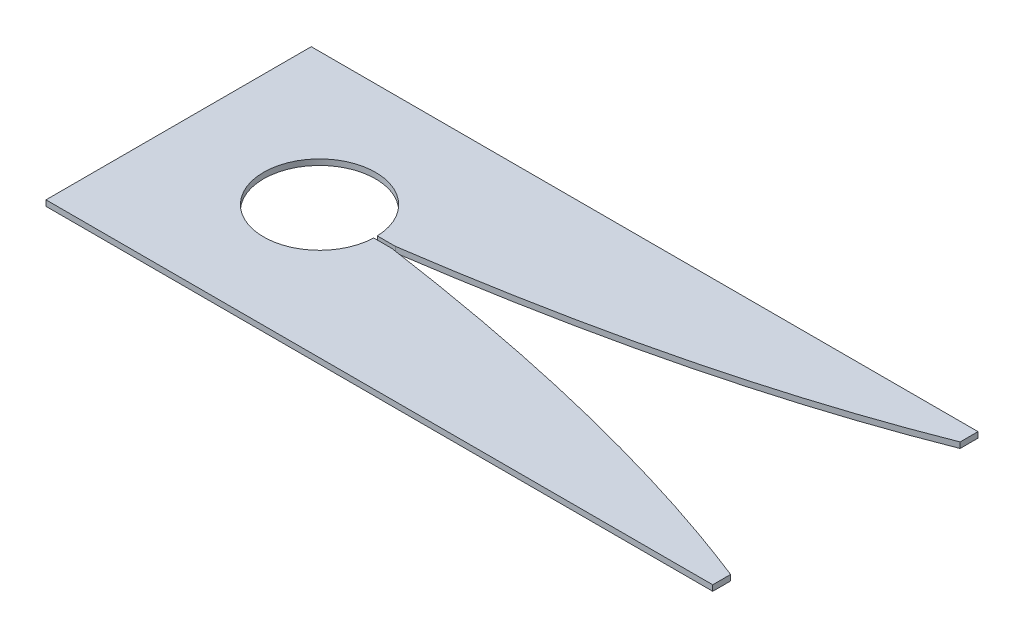
SolidWorks part; units mm, degrees
ref_plane "Front" through (0, 0, 0) normal (0, 0, 1) x (1, 0, 0)
ref_plane "Top" through (0, 0, 0) normal (0, 1, 0) x (1, 0, 0)
ref_plane "Right" through (0, 0, 0) normal (1, 0, 0) x (0, 0, -1)
sketch "Sketch1" plane through (0, 0, 0) normal (0, 1, 0) x (1, 0, 0)
  line L0 (-92.9999, -37.0001) -> (92.9999, -37.0001)
  line L1 (-92.9999, -37.0001) -> (-92.9999, 37.0001)
  line L2 (92.9999, -37.0001) -> (92.9999, 37.0001)
  line L3 (-92.9999, 37.0001) -> (92.9999, 37.0001)
  line L4 (-92.9999, -37.0001) -> (92.9999, 37.0001) construction
  line L5 (92.9999, -37.0001) -> (-92.9999, 37.0001) construction
  line L6 (92.964, 31.75) -> (92.964, -31.75)
  line L7 (-33.02, -0.9971) -> (-37.093, -0.9971)
  line L8 (-37.093, -0.9971) -> (-37.093, 0.9971)
  line L9 (-37.093, 0.9971) -> (-33.02, 0.9971)
  spline S0 degree 4 poles (-45.6197, -0.7148) (-45.419, -0.6888) (-45.0217, -0.6373) (-44.2575, -0.5383) (-42.6269, -0.3238) (-40.5686, -0.051) (-38.0308, 0.2948) (-35.9146, 0.5872) (-33.3422, 0.9506) (-32.1764, 1.1175) (-29.311, 1.5318) (-27.5556, 1.794) (-24.9918, 2.1776) (-22.9161, 2.4977) (-20.5474, 2.8657) (-18.3562, 3.2147) (-16.0618, 3.5849) (-13.8271, 3.953) (-10.9989, 4.4264) (-7.6266, 5.0049) (-3.6838, 5.7012) (0.8099, 6.5235) (5.3023, 7.3751) (9.7867, 8.2559) (14.2664, 9.1672) (18.7388, 10.1098) (23.2047, 11.0847) (28.1443, 12.2016) (33.0741, 13.3618) (37.9931, 14.5667) (42.9005, 15.8179) (47.32, 16.9846) (51.7292, 18.1898) (56.1275, 19.4344) (59.9658, 20.5588) (63.2481, 21.5485) (66.5238, 22.5591) (69.7932, 23.5911) (73.0534, 24.6499) (76.0345, 25.6462) (78.1969, 26.3834) (79.8188, 26.9427) (81.434, 27.5058) (83.3257, 28.1752) (85.4657, 28.9448) (87.3602, 29.6383) (88.9415, 30.2247) (90.3224, 30.7433) (91.291, 31.1093) (92.7461, 31.6655) (93.5084, 31.9594) (95.4183, 32.7008) (96.5717, 33.1584) (98.2705, 33.8329) (99.6393, 34.3874) (101.2218, 35.0314) (102.4786, 35.5521) (103.6359, 36.0337) (104.3677, 36.342) (104.7445, 36.5009) (104.9341, 36.581) knots 0 0 0 0 0 0.005108 0.010215 0.02043 0.040861 0.061291 0.071506 0.081722 0.096411 0.111101 0.125791 0.140481 0.155171 0.169861 0.18455 0.19924 0.21393 0.22862 0.258 0.287379 0.316759 0.346139 0.375518 0.404898 0.434278 0.463657 0.493037 0.535103 0.564483 0.593863 0.623242 0.652622 0.682002 0.711381 0.726071 0.740761 0.770141 0.799521 0.81421 0.821555 0.8289 0.84359 0.85828 0.87297 0.88766 0.895004 0.902349 0.909694 0.917039 0.927346 0.937653 0.94796 0.958267 0.9687 0.979133 0.989567 0.994783 1 1 1 1 1 construction
  spline S1 degree 4 poles (-33.02, 0.9971) (-32.5475, 1.0646) (-31.6372, 1.1955) (-29.311, 1.5318) (-27.5556, 1.794) (-24.9918, 2.1776) (-22.9161, 2.4977) (-20.5474, 2.8657) (-18.3562, 3.2147) (-16.0618, 3.5849) (-13.8271, 3.953) (-10.9989, 4.4264) (-7.6266, 5.0049) (-3.6838, 5.7012) (0.8099, 6.5235) (5.3023, 7.3751) (9.7867, 8.2559) (14.2664, 9.1672) (18.7388, 10.1098) (23.2047, 11.0847) (28.1443, 12.2016) (33.0741, 13.3618) (37.9931, 14.5667) (42.9005, 15.8179) (47.32, 16.9846) (51.7292, 18.1898) (56.1275, 19.4344) (59.9658, 20.5588) (63.2481, 21.5485) (66.5238, 22.5591) (69.7932, 23.5911) (73.0534, 24.6499) (76.0345, 25.6462) (78.1969, 26.3834) (79.8188, 26.9427) (81.434, 27.5058) (83.3257, 28.1752) (85.4657, 28.9448) (87.3602, 29.6383) (88.9415, 30.2247) (90.3224, 30.7433) (91.291, 31.1093) (92.2824, 31.4882) (92.7413, 31.6643) (92.964, 31.75) knots 0.081722 0.081722 0.081722 0.081722 0.081722 0.096411 0.111101 0.125791 0.140481 0.155171 0.169861 0.18455 0.19924 0.21393 0.22862 0.258 0.287379 0.316759 0.346139 0.375518 0.404898 0.434278 0.463657 0.493037 0.535103 0.564483 0.593863 0.623242 0.652622 0.682002 0.711381 0.726071 0.740761 0.770141 0.799521 0.81421 0.821555 0.8289 0.84359 0.85828 0.87297 0.88766 0.895004 0.902349 0.909694 0.917039 0.917039 0.917039 0.917039 0.917039
  spline S2 degree 4 poles (-45.6197, 0.7148) (-45.419, 0.6888) (-45.0217, 0.6373) (-44.2575, 0.5383) (-42.6269, 0.3238) (-40.5686, 0.051) (-38.0308, -0.2948) (-35.9146, -0.5872) (-33.3422, -0.9506) (-32.1764, -1.1175) (-29.311, -1.5318) (-27.5556, -1.794) (-24.9918, -2.1776) (-22.9161, -2.4977) (-20.5474, -2.8657) (-18.3562, -3.2147) (-16.0618, -3.5849) (-13.8271, -3.953) (-10.9989, -4.4264) (-7.6266, -5.0049) (-3.6838, -5.7012) (0.8099, -6.5235) (5.3023, -7.3751) (9.7867, -8.2559) (14.2664, -9.1672) (18.7388, -10.1098) (23.2047, -11.0847) (28.1443, -12.2016) (33.0741, -13.3618) (37.9931, -14.5667) (42.9005, -15.8179) (47.32, -16.9846) (51.7292, -18.1898) (56.1275, -19.4344) (59.9658, -20.5588) (63.2481, -21.5485) (66.5238, -22.5591) (69.7932, -23.5911) (73.0534, -24.6499) (76.0345, -25.6462) (78.1969, -26.3834) (79.8188, -26.9427) (81.434, -27.5058) (83.3257, -28.1752) (85.4657, -28.9448) (87.3602, -29.6383) (88.9415, -30.2247) (90.3224, -30.7433) (91.291, -31.1093) (92.7461, -31.6655) (93.5084, -31.9594) (95.4183, -32.7008) (96.5717, -33.1584) (98.2705, -33.8329) (99.6393, -34.3874) (101.2218, -35.0314) (102.4786, -35.5521) (103.6359, -36.0337) (104.3677, -36.342) (104.7445, -36.5009) (104.9341, -36.581) knots 0 0 0 0 0 0.005108 0.010215 0.02043 0.040861 0.061291 0.071506 0.081722 0.096411 0.111101 0.125791 0.140481 0.155171 0.169861 0.18455 0.19924 0.21393 0.22862 0.258 0.287379 0.316759 0.346139 0.375518 0.404898 0.434278 0.463657 0.493037 0.535103 0.564483 0.593863 0.623242 0.652622 0.682002 0.711381 0.726071 0.740761 0.770141 0.799521 0.81421 0.821555 0.8289 0.84359 0.85828 0.87297 0.88766 0.895004 0.902349 0.909694 0.917039 0.927346 0.937653 0.94796 0.958267 0.9687 0.979133 0.989567 0.994783 1 1 1 1 1 construction
  spline S3 degree 4 poles (-33.02, -0.9971) (-32.5475, -1.0646) (-31.6372, -1.1955) (-29.311, -1.5318) (-27.5556, -1.794) (-24.9918, -2.1776) (-22.9161, -2.4977) (-20.5474, -2.8657) (-18.3562, -3.2147) (-16.0618, -3.5849) (-13.8271, -3.953) (-10.9989, -4.4264) (-7.6266, -5.0049) (-3.6838, -5.7012) (0.8099, -6.5235) (5.3023, -7.3751) (9.7867, -8.2559) (14.2664, -9.1672) (18.7388, -10.1098) (23.2047, -11.0847) (28.1443, -12.2016) (33.0741, -13.3618) (37.9931, -14.5667) (42.9005, -15.8179) (47.32, -16.9846) (51.7292, -18.1898) (56.1275, -19.4344) (59.9658, -20.5588) (63.2481, -21.5485) (66.5238, -22.5591) (69.7932, -23.5911) (73.0534, -24.6499) (76.0345, -25.6462) (78.1969, -26.3834) (79.8188, -26.9427) (81.434, -27.5058) (83.3257, -28.1752) (85.4657, -28.9448) (87.3602, -29.6383) (88.9415, -30.2247) (90.3224, -30.7433) (91.291, -31.1093) (92.2824, -31.4882) (92.7413, -31.6643) (92.964, -31.75) knots 0.081722 0.081722 0.081722 0.081722 0.081722 0.096411 0.111101 0.125791 0.140481 0.155171 0.169861 0.18455 0.19924 0.21393 0.22862 0.258 0.287379 0.316759 0.346139 0.375518 0.404898 0.434278 0.463657 0.493037 0.535103 0.564483 0.593863 0.623242 0.652622 0.682002 0.711381 0.726071 0.740761 0.770141 0.799521 0.81421 0.821555 0.8289 0.84359 0.85828 0.87297 0.88766 0.895004 0.902349 0.909694 0.917039 0.917039 0.917039 0.917039 0.917039
  point P1 (0, 0)
  dimension "D1" = 74.0001
  dimension "D2" = 185.9999
extrude "Boss-Extrude3" add sketch "Sketch1" along normal blind 1.5875 contours L0 L2 L3 L1
sketch "Sketch4" plane through (0, 1.5875, 0) normal (0, 1, 0) x (1, 0, 0)
  line L0 (-33.02, 0.5) -> (-38.0763, 0.5)
  line L1 (92.964, 31.9999) -> (94.1908, 31.9999)
  line L2 (-38.0763, -0.5) -> (-33.02, -0.5)
  line L3 (94.1908, 31.9999) -> (94.1908, -31.9999)
  line L4 (94.1908, -31.9999) -> (92.964, -31.9999)
  arc A0 (-38.0763, 0.5) -> (-38.0763, -0.5) centre (-53.6893, 0) ccw
  spline S0 degree 4 poles (-45.6216, -1.2538) (-45.4152, -1.2264) (-45.0124, -1.1728) (-44.2886, -1.0772) (-42.5574, -0.8429) (-41.0656, -0.6424) (-38.7059, -0.3125) (-36.8776, -0.0578) (-33.8387, 0.38) (-32.6102, 0.5588) (-29.371, 1.0389) (-27.4951, 1.3252) (-25.0001, 1.7081) (-22.8724, 2.0437) (-20.5264, 2.4175) (-18.3124, 2.7785) (-16.0227, 3.1572) (-13.7765, 3.5362) (-10.9454, 4.0219) (-6.4335, 4.815) (-1.3567, 5.7445) (4.2702, 6.8248) (11.0135, 8.1823) (16.6209, 9.3655) (22.2175, 10.6032) (28.2313, 11.9974) (33.1186, 13.1762) (37.9946, 14.3998) (42.8589, 15.6697) (47.2851, 16.8662) (51.7006, 18.1021) (56.1045, 19.3784) (59.9473, 20.5313) (63.233, 21.5458) (65.9655, 22.4093) (68.148, 23.1109) (70.8719, 24.0017) (73.5891, 24.9108) (76.0299, 25.7463) (78.1934, 26.5017) (79.8162, 27.0749) (81.432, 27.652) (83.3244, 28.3378) (85.4651, 29.1263) (87.3598, 29.8368) (88.9416, 30.4376) (90.3222, 30.9687) (91.2914, 31.3438) (92.7462, 31.9134) (93.5086, 32.2146) (95.4193, 32.9742) (96.5725, 33.4429) (98.2719, 34.1339) (99.6403, 34.7018) (101.2229, 35.3615) (102.4792, 35.8946) (103.6365, 36.388) (104.3678, 36.7035) (104.7446, 36.8663) (104.9341, 36.9483) knots 0 0 0 0 0 0.005102 0.010204 0.020408 0.040816 0.05102 0.061223 0.081631 0.096344 0.111056 0.125769 0.140481 0.155194 0.169906 0.184619 0.199331 0.214044 0.228757 0.258182 0.317032 0.346457 0.375882 0.434732 0.464157 0.493582 0.534357 0.563782 0.593207 0.622632 0.652057 0.681483 0.710908 0.72562 0.740333 0.755045 0.769758 0.799183 0.813895 0.821252 0.828608 0.84332 0.858033 0.872745 0.887458 0.894814 0.90217 0.909527 0.916883 0.92721 0.937537 0.947864 0.958191 0.968643 0.979096 0.989548 0.994774 1 1 1 1 1 construction
  spline S1 degree 4 poles (-33.02, 0.5) (-32.5463, 0.5692) (-31.586, 0.7106) (-29.371, 1.0389) (-27.4951, 1.3252) (-25.0001, 1.7081) (-22.8724, 2.0437) (-20.5264, 2.4175) (-18.3124, 2.7785) (-16.0227, 3.1572) (-13.7765, 3.5362) (-10.9454, 4.0219) (-6.4335, 4.815) (-1.3567, 5.7445) (4.2702, 6.8248) (11.0135, 8.1823) (16.6209, 9.3655) (22.2175, 10.6032) (28.2313, 11.9974) (33.1186, 13.1762) (37.9946, 14.3998) (42.8589, 15.6697) (47.2851, 16.8662) (51.7006, 18.1021) (56.1045, 19.3784) (59.9473, 20.5313) (63.233, 21.5458) (65.9655, 22.4093) (68.148, 23.1109) (70.8719, 24.0017) (73.5891, 24.9108) (76.0299, 25.7463) (78.1934, 26.5017) (79.8162, 27.0749) (81.432, 27.652) (83.3244, 28.3378) (85.4651, 29.1263) (87.3598, 29.8368) (88.9416, 30.4376) (90.3222, 30.9687) (91.2914, 31.3438) (92.2825, 31.7319) (92.7413, 31.9122) (92.964, 31.9999) knots 0.081631 0.081631 0.081631 0.081631 0.081631 0.096344 0.111056 0.125769 0.140481 0.155194 0.169906 0.184619 0.199331 0.214044 0.228757 0.258182 0.317032 0.346457 0.375882 0.434732 0.464157 0.493582 0.534357 0.563782 0.593207 0.622632 0.652057 0.681483 0.710908 0.72562 0.740333 0.755045 0.769758 0.799183 0.813895 0.821252 0.828608 0.84332 0.858033 0.872745 0.887458 0.894814 0.90217 0.909527 0.916883 0.916883 0.916883 0.916883 0.916883
  spline S2 degree 4 poles (-45.6216, 1.2538) (-45.4152, 1.2264) (-45.0124, 1.1728) (-44.2886, 1.0772) (-42.5574, 0.8429) (-41.0656, 0.6424) (-38.7059, 0.3125) (-36.8776, 0.0578) (-33.8387, -0.38) (-32.6102, -0.5588) (-29.371, -1.0389) (-27.4951, -1.3252) (-25.0001, -1.7081) (-22.8724, -2.0437) (-20.5264, -2.4175) (-18.3124, -2.7785) (-16.0227, -3.1572) (-13.7765, -3.5362) (-10.9454, -4.0219) (-6.4335, -4.815) (-1.3567, -5.7445) (4.2702, -6.8248) (11.0135, -8.1823) (16.6209, -9.3655) (22.2175, -10.6032) (28.2313, -11.9974) (33.1186, -13.1762) (37.9946, -14.3998) (42.8589, -15.6697) (47.2851, -16.8662) (51.7006, -18.1021) (56.1045, -19.3784) (59.9473, -20.5313) (63.233, -21.5458) (65.9655, -22.4093) (68.148, -23.1109) (70.8719, -24.0017) (73.5891, -24.9108) (76.0299, -25.7463) (78.1934, -26.5017) (79.8162, -27.0749) (81.432, -27.652) (83.3244, -28.3378) (85.4651, -29.1263) (87.3598, -29.8368) (88.9416, -30.4376) (90.3222, -30.9687) (91.2914, -31.3438) (92.7462, -31.9134) (93.5086, -32.2146) (95.4193, -32.9742) (96.5725, -33.4429) (98.2719, -34.1339) (99.6403, -34.7018) (101.2229, -35.3615) (102.4792, -35.8946) (103.6365, -36.388) (104.3678, -36.7035) (104.7446, -36.8663) (104.9341, -36.9483) knots 0 0 0 0 0 0.005102 0.010204 0.020408 0.040816 0.05102 0.061223 0.081631 0.096344 0.111056 0.125769 0.140481 0.155194 0.169906 0.184619 0.199331 0.214044 0.228757 0.258182 0.317032 0.346457 0.375882 0.434732 0.464157 0.493582 0.534357 0.563782 0.593207 0.622632 0.652057 0.681483 0.710908 0.72562 0.740333 0.755045 0.769758 0.799183 0.813895 0.821252 0.828608 0.84332 0.858033 0.872745 0.887458 0.894814 0.90217 0.909527 0.916883 0.92721 0.937537 0.947864 0.958191 0.968643 0.979096 0.989548 0.994774 1 1 1 1 1 construction
  spline S3 degree 4 poles (-33.02, -0.5) (-32.5463, -0.5692) (-31.586, -0.7106) (-29.371, -1.0389) (-27.4951, -1.3252) (-25.0001, -1.7081) (-22.8724, -2.0437) (-20.5264, -2.4175) (-18.3124, -2.7785) (-16.0227, -3.1572) (-13.7765, -3.5362) (-10.9454, -4.0219) (-6.4335, -4.815) (-1.3567, -5.7445) (4.2702, -6.8248) (11.0135, -8.1823) (16.6209, -9.3655) (22.2175, -10.6032) (28.2313, -11.9974) (33.1186, -13.1762) (37.9946, -14.3998) (42.8589, -15.6697) (47.2851, -16.8662) (51.7006, -18.1021) (56.1045, -19.3784) (59.9473, -20.5313) (63.233, -21.5458) (65.9655, -22.4093) (68.148, -23.1109) (70.8719, -24.0017) (73.5891, -24.9108) (76.0299, -25.7463) (78.1934, -26.5017) (79.8162, -27.0749) (81.432, -27.652) (83.3244, -28.3378) (85.4651, -29.1263) (87.3598, -29.8368) (88.9416, -30.4376) (90.3222, -30.9687) (91.2914, -31.3438) (92.2825, -31.7319) (92.7413, -31.9122) (92.964, -31.9999) knots 0.081631 0.081631 0.081631 0.081631 0.081631 0.096344 0.111056 0.125769 0.140481 0.155194 0.169906 0.184619 0.199331 0.214044 0.228757 0.258182 0.317032 0.346457 0.375882 0.434732 0.464157 0.493582 0.534357 0.563782 0.593207 0.622632 0.652057 0.681483 0.710908 0.72562 0.740333 0.755045 0.769758 0.799183 0.813895 0.821252 0.828608 0.84332 0.858033 0.872745 0.887458 0.894814 0.90217 0.909527 0.916883 0.916883 0.916883 0.916883 0.916883
extrude "Cut-Extrude3" cut sketch "Sketch4" against normal blind 2.54
